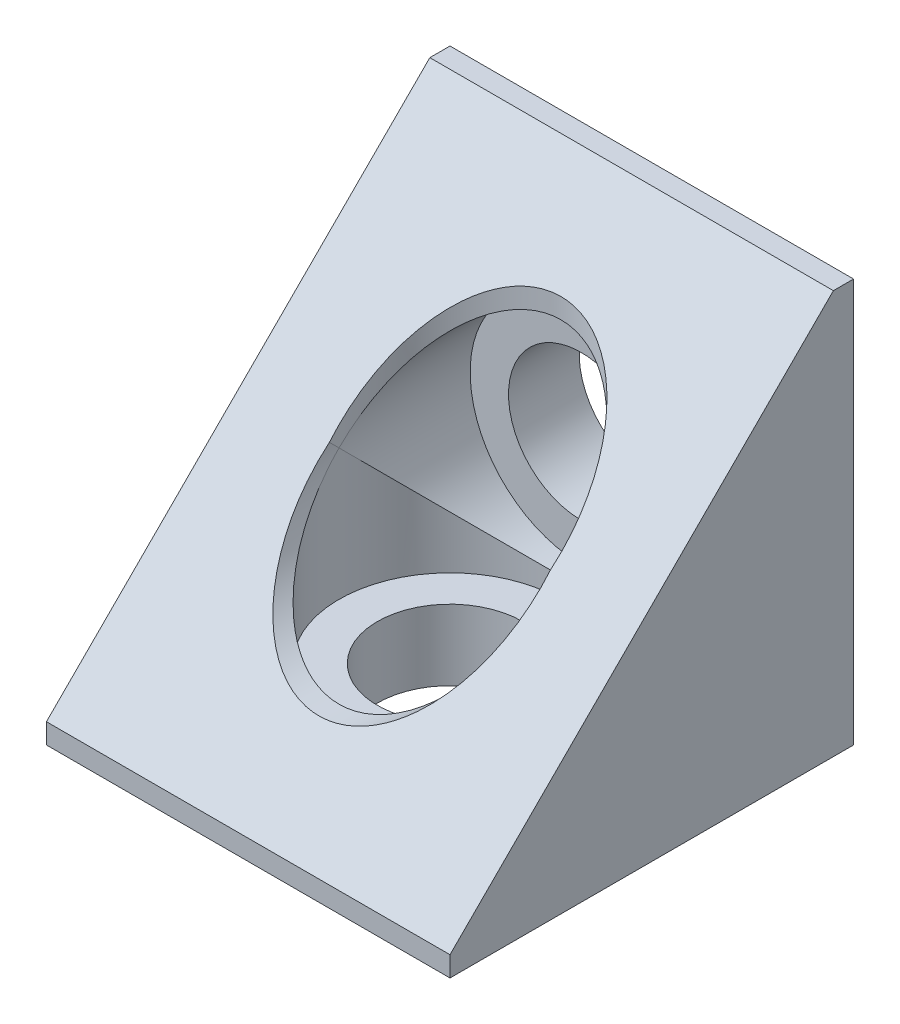
SolidWorks part; units mm, degrees
material "ABS"
ref_plane "Front Plane" through (0, 0, 0) normal (0, 0, 1) x (1, 0, 0)
ref_plane "Top Plane" through (0, 0, 0) normal (0, 1, 0) x (1, 0, 0)
ref_plane "Right Plane" through (0, 0, 0) normal (1, 0, 0) x (0, 0, -1)
other "grey"
ref_plane "Plane1" through (-10, 0, 0) normal (-1, 0, 0) x (0, -1, 0)
sketch "Sketch1" plane through (-10, 0, 0) normal (-1, 0, 0) x (0, -1, 0)
  line L0 (9, 10) -> (-10, -9)
  line L1 (-10, -9) -> (-10, -10)
  line L2 (-10, -10) -> (10, -10)
  line L3 (10, -10) -> (10, 10)
  line L4 (10, 10) -> (9, 10)
extrude "Boss-Extrude1" add sketch "Sketch1" against normal blind 20
sketch "Sketch2" plane through (0, 0, 0) normal (1, 0, 0) x (0, 0, -1)
  line L0 (5.5, 6.5) -> (0, 6.5)
  line L1 (0, 6.5) -> (0, -10)
  line L2 (0, -10) -> (3.6, -10)
  line L3 (3.6, -10) -> (3.6, -6.5)
  line L4 (3.6, -6.5) -> (5.5, -6.5)
  line L5 (5.5, -6.5) -> (5.5, 6.5)
  line L6 (0, 6.5) -> (0, -10) construction
revolve "Cut-Revolve1" cut sketch "Sketch2" angle 360 about L6
ref_plane "Plane2" through (0, 0, 6.5) normal (0, 0, 1) x (1, 0, 0)
hole_wizard "Hole1" positions "Sketch4" profile "Sketch3" legacy
sketch "Sketch4" plane through (0, 0, 6.5) normal (0, 0, 1) x (1, 0, 0)
  point P0 (0, 0)
sketch "Sketch3" plane through (0, 0, 6.5) normal (1, 0, 0) x (0, -1, 0)
  line L0 (0, 0) -> (0, 16.5)
  line L1 (0, 16.5) -> (3.6, 16.5)
  line L2 (3.6, 16.5) -> (3.6, 13)
  line L3 (3.6, 13) -> (5.5, 13)
  line L4 (5.5, 13) -> (5.5, 0)
  line L5 (5.5, 0) -> (0, 0)
  line L6 (0, 110) -> (0, -10) construction
  dimension "Diameter" = 7.2
  dimension "Depth" = 16.5
  dimension "C-Bore Diameter" = 11
  dimension "C-Bore Depth" = 13
